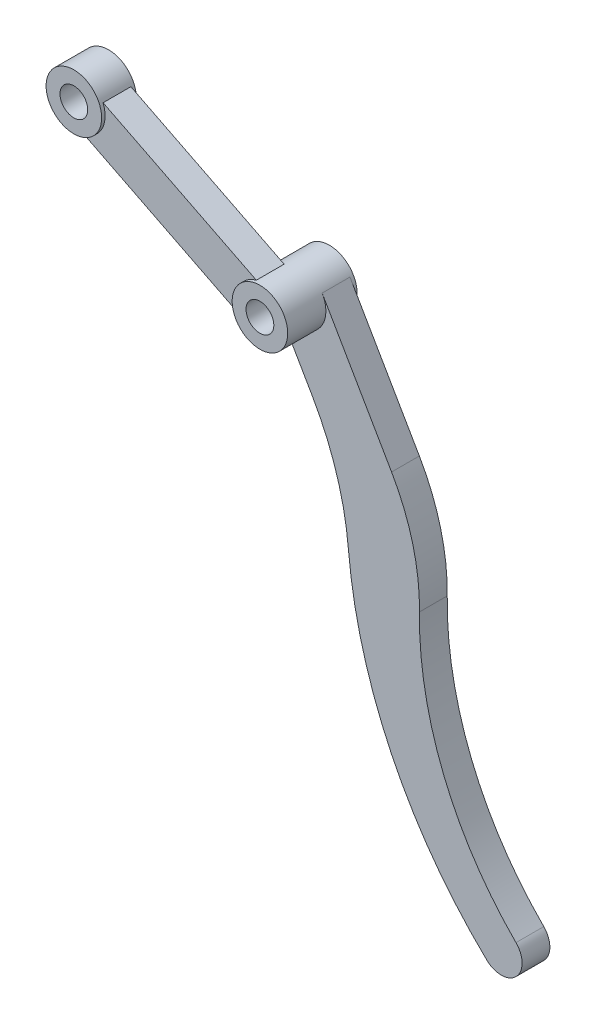
SolidWorks part; units mm, degrees
ref_plane "前视基准面" through (0, 0, 0) normal (0, 0, 1) x (1, 0, 0)
ref_plane "上视基准面" through (0, 0, 0) normal (0, 1, 0) x (1, 0, 0)
ref_plane "右视基准面" through (0, 0, 0) normal (1, 0, 0) x (0, 0, -1)
sketch "草图1" plane through (0, 0, 0) normal (0, 0, 1) x (1, 0, 0)
  circle A0 centre (0, 0) radius 4
  circle A1 centre (0, 0) radius 8
  circle A2 centre (-53.606, 26.9518) radius 4
  circle A3 centre (-53.606, 26.9518) radius 8
  dimension "D1" = 8
  dimension "D2" = 16
  dimension "D3" = 60
extrude "凸台-拉伸1" add sketch "草图1" along normal blind 10
sketch "草图3" plane through (0, 0, 0) normal (0, 0, 1) x (1, 0, 0)
  line L0 (-53.606, 26.9518) -> (0, 0) construction
  line L1 (-51.5735, 19.2143) -> (-7.4228, -2.9837)
  line L2 (-46.1832, 29.9355) -> (-2.0324, 7.7375)
  line L4 (-50.9108, 32.3124) -> (2.6952, 5.3606) construction
  line L5 (-56.3011, 21.5912) -> (-2.6952, -5.3606) construction
  circle A0 centre (0, 0) radius 8 construction
  circle A1 centre (-53.606, 26.9518) radius 8 construction
  arc A2 (-2.0324, 7.7375) -> (-7.4228, -2.9837) centre (0, 0) ccw
  arc A3 (-51.5735, 19.2143) -> (-46.1832, 29.9355) centre (-53.606, 26.9518) ccw
  dimension "D1" = 6
  dimension "D2" = 6
extrude "凸台-拉伸2" add sketch "草图3" along normal blind 8 from offset 1 contours A2 L1 A3 L2
sketch "草图4" plane through (0, 0, 0) normal (0, 0, 1) x (1, 0, 0)
  line L0 (8, 0) -> (8, -40) construction
  line L1 (-8, 0) -> (-8, -22) construction
  line L2 (81.0592, -119.5) -> (81.0592, -87.7121) construction
  line L3 (-16.4993, -145.6407) -> (81.0592, -119.5) construction
  line L4 (6.9282, 4) -> (26.9282, -30.641)
  line L5 (-6.9282, -4) -> (4.0718, -23.0526)
  line L6 (129.9493, -62.9604) -> (114.0553, -35.4313) construction
  line L7 (58.5315, -134.3782) -> (129.9493, -62.9604) construction
  circle A0 centre (0, 0) radius 8 construction
  arc A1 (-2.0324, 7.7375) -> (-7.4228, -2.9837) centre (0, 0) ccw construction
  arc A2 (-8, -22) -> (-15.4566, -55.7262) centre (-88, -22) cw construction
  arc A3 (-15.4566, -55.7262) -> (-22.2538, -147.3396) centre (102.4264, -110.5313) ccw construction
  arc A4 (-22.2538, -147.3396) -> (-10.7038, -144.0878) centre (-16.4993, -145.6407) ccw construction
  arc A5 (-10.7038, -144.0878) -> (-0.4932, -70.7742) centre (81.0592, -119.5) cw construction
  arc A6 (-0.4932, -70.7742) -> (8, -40) centre (-52, -40) ccw construction
  arc A7 (-6.9282, -4) -> (8, 0) centre (0, 0) ccw construction
  arc A8 (4.0718, -23.0526) -> (14.4773, -55.9886) centre (-65.2102, -63.0526) cw
  arc A9 (14.4773, -55.9886) -> (54.3974, -138.7267) centre (143.9695, -44.5097) ccw
  arc A10 (54.3974, -138.7267) -> (62.7742, -130.1356) centre (58.5315, -134.3782) ccw
  arc A11 (62.7742, -130.1356) -> (34.96, -61.5389) centre (129.9493, -62.9604) cw
  arc A12 (34.96, -61.5389) -> (26.9282, -30.641) centre (-25.0333, -60.641) ccw
  arc A13 (-6.9282, -4) -> (6.9282, 4) centre (0, 0) ccw construction
  arc A14 (-6.9282, -4) -> (6.9282, 4) centre (0, 0) ccw
  dimension "D3" = 95
  dimension "D4" = 130
  dimension "D5" = 6
  dimension "D6" = 80
  dimension "D7" = 60
  dimension "D8" = 119.5
  dimension "D1" = 22
  dimension "D2" = 40
  dimension "D9" = 105
  dimension "D10" = 2
extrude "凸台-拉伸3" add sketch "草图4" against normal blind 8 from offset 1 offset against normal yes
sketch "草图5" plane through (0, 0, 0) normal (0, 0, 1) x (1, 0, 0)
  circle A0 centre (0, 0) radius 8 construction
  circle A1 centre (0, 0) radius 4 construction
  circle A2 centre (0, 0) radius 8
  circle A3 centre (0, 0) radius 4
extrude "凸台-拉伸4" add sketch "草图5" against normal blind 10
